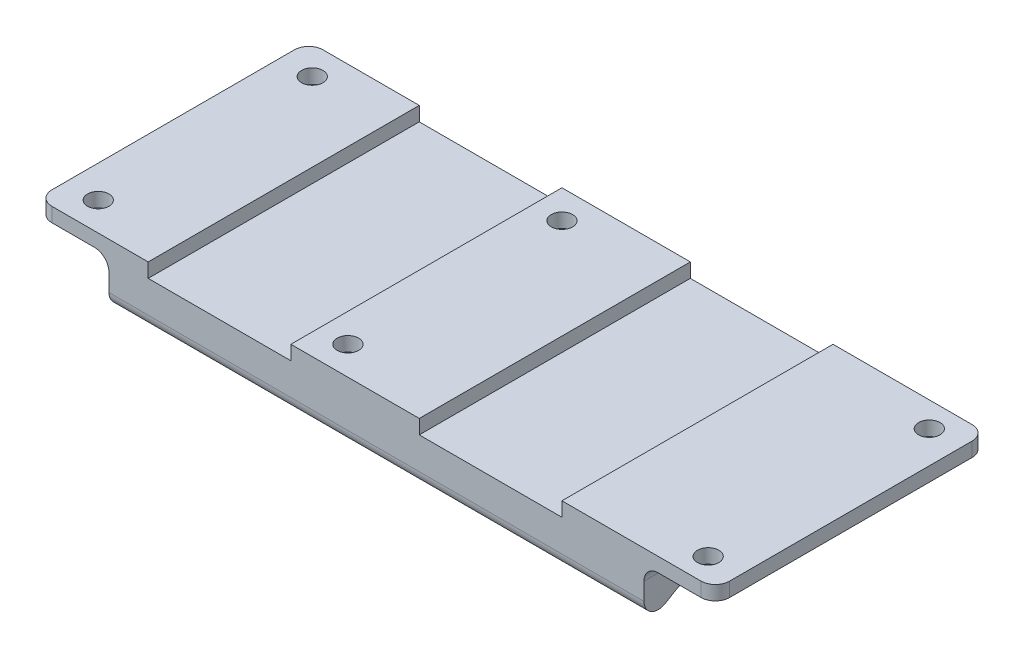
SolidWorks part; units mm, degrees
material "PEI"
ref_plane "Front Plane" through (0, 0, 0) normal (0, 0, 1) x (1, 0, 0)
ref_plane "Top Plane" through (0, 0, 0) normal (0, 1, 0) x (1, 0, 0)
ref_plane "Right Plane" through (0, 0, 0) normal (1, 0, 0) x (0, 0, -1)
sketch "Sketch1" plane through (0, 0, 0) normal (0, 1, 0) x (1, 0, 0)
  line L1 (45.5, -19) -> (-29.5, -19)
  line L2 (45.5, -19) -> (45.5, 19)
  line L3 (45.5, 19) -> (-29.5, 19)
  line L4 (-29.5, -19) -> (-29.5, 19)
  line L5 (45.5, -19) -> (-29.5, 19) construction
  line L6 (45.5, 19) -> (-29.5, -19) construction
  point P0 (8, 0)
  point P6 (0, 0)
  point P7 (14.5588, 3.1563)
  point P9 (0, 0)
  dimension "D1" = 38
  dimension "D2" = 75
  dimension "D3" = 8
extrude "Boss-Extrude1" add sketch "Sketch1" against normal blind 10
sketch "Sketch2" plane through (45.5, 0, 0) normal (1, 0, 0) x (0, 0, -1)
  line L0 (-19, -10) -> (-14, -7)
  line L1 (-14, -7) -> (14, -7)
  line L2 (0, -7) -> (0, -10)
  line L3 (19, -10) -> (14, -7)
  line L4 (19, 0) -> (-19, 0)
  line L5 (-19, 0) -> (-19, -10)
  line L6 (-19, -10) -> (19, -10)
  line L7 (19, -10) -> (19, 0)
  line L8 (19, 0) -> (-19, 0)
  line L9 (-19, 0) -> (-19, -10)
  line L10 (-19, -10) -> (19, -10)
  line L11 (19, -10) -> (19, 0)
  line M7 (-19, -10) -> (19, -10)
  dimension "D2" = 5
  dimension "D3" = 3
  dimension "D1" = 0
extrude "Cut-Extrude1" cut sketch "Sketch2" against normal through all and the other way through all contours L2 L1 L0 M7 | L3 L1 L2 M7
fillet "Fillet1" radius 2 4 edges at (8, -7, 14) (8, -7, -14) (8, -10, -19) (8, -10, 19)
sketch "Sketch4" plane through (-29.5, 0, 0) normal (-1, 0, 0) x (0, 0, 1)
  line L1 (-19, 0) -> (19, 0)
  line L2 (-19, 0) -> (-19, -2)
  line L3 (-19, -2) -> (19, -2)
  line L4 (19, 0) -> (19, -2)
  line L6 (-19, 0) -> (-19, -6.4676)
  line L7 (-15.971, -8.1826) -> (-14.475, -7.285)
  line L11 (19, 0) -> (-19, 0)
  line L12 (-19, 0) -> (-19, -6.4676)
  line L13 (-15.971, -8.1826) -> (-14.475, -7.285)
  line L17 (19, 0) -> (-19, 0)
  line L19 (-13.446, -7) -> (13.446, -7)
  line L20 (-13.446, -7) -> (13.446, -7)
  line L21 (14.475, -7.285) -> (15.971, -8.1826)
  line L22 (14.475, -7.285) -> (15.971, -8.1826)
  line L23 (19, -6.4676) -> (19, 0)
  line L24 (19, -6.4676) -> (19, 0)
  arc A4 (-19, -6.4676) -> (-15.971, -8.1826) centre (-17, -6.4676) ccw
  arc A5 (-19, -6.4676) -> (-15.971, -8.1826) centre (-17, -6.4676) ccw
  arc A6 (-13.446, -7) -> (-14.475, -7.285) centre (-13.446, -9) ccw
  arc A7 (-13.446, -7) -> (-14.475, -7.285) centre (-13.446, -9) ccw
  arc A12 (14.475, -7.285) -> (13.446, -7) centre (13.446, -9) ccw
  arc A13 (14.475, -7.285) -> (13.446, -7) centre (13.446, -9) ccw
  arc A14 (15.971, -8.1826) -> (19, -6.4676) centre (17, -6.4676) ccw
  arc A15 (15.971, -8.1826) -> (19, -6.4676) centre (17, -6.4676) ccw
  line M12 (-19, 0) -> (-19, -6.4676)
  line M20 (19, -6.4676) -> (19, 0)
  line M21 (19, 0) -> (-19, 0)
  dimension "D2" = 2
  dimension "D1" = 0
extrude "Boss-Extrude2" add sketch "Sketch4" along normal blind 10 contours L3 M12 M20 M21
sketch "Sketch5" plane through (45.5, 0, 0) normal (1, 0, 0) x (0, 0, -1)
  line L1 (-19, 0) -> (19, 0)
  line L2 (-19, 0) -> (-19, -2)
  line L3 (-19, -2) -> (19, -2)
  line L4 (19, 0) -> (19, -2)
  line L6 (14.475, -7.285) -> (15.971, -8.1826)
  line L7 (19, -6.4676) -> (19, 0)
  line L8 (19, 0) -> (-19, 0)
  line L12 (14.475, -7.285) -> (15.971, -8.1826)
  line L13 (19, -6.4676) -> (19, 0)
  line L14 (19, 0) -> (-19, 0)
  line L19 (-19, 0) -> (-19, -6.4676)
  line L20 (-19, 0) -> (-19, -6.4676)
  line L21 (-15.971, -8.1826) -> (-14.475, -7.285)
  line L22 (-15.971, -8.1826) -> (-14.475, -7.285)
  line L23 (-13.446, -7) -> (13.446, -7)
  line L24 (-13.446, -7) -> (13.446, -7)
  arc A4 (15.971, -8.1826) -> (19, -6.4676) centre (17, -6.4676) ccw
  arc A5 (15.971, -8.1826) -> (19, -6.4676) centre (17, -6.4676) ccw
  arc A6 (-19, -6.4676) -> (-15.971, -8.1826) centre (-17, -6.4676) ccw
  arc A7 (-19, -6.4676) -> (-15.971, -8.1826) centre (-17, -6.4676) ccw
  arc A12 (-13.446, -7) -> (-14.475, -7.285) centre (-13.446, -9) ccw
  arc A13 (-13.446, -7) -> (-14.475, -7.285) centre (-13.446, -9) ccw
  arc A14 (14.475, -7.285) -> (13.446, -7) centre (13.446, -9) ccw
  arc A15 (14.475, -7.285) -> (13.446, -7) centre (13.446, -9) ccw
  line M14 (19, -6.4676) -> (19, 0)
  line M15 (19, 0) -> (-19, 0)
  line M16 (-19, 0) -> (-19, -6.4676)
  dimension "D2" = 2
  dimension "D1" = 0
extrude "Boss-Extrude3" add sketch "Sketch5" along normal blind 10 contours L3 M16 M14 M15
sketch "Sketch6" plane through (0, 0, 0) normal (0, 1, 0) x (1, 0, 0)
  line L0 (0, 0) -> (55.5, 0)
  line L1 (51, 0) -> (51, 15.5)
  line L2 (0, 0) -> (0, 15)
  line L3 (0, 15) -> (-35, 15)
  line L4 (55.5, 19) -> (-39.5, 19)
  line L5 (-39.5, 19) -> (-39.5, -19)
  line L6 (-39.5, -19) -> (55.5, -19)
  line L7 (55.5, -19) -> (55.5, 19)
  line L8 (55.5, 19) -> (-39.5, 19)
  line L9 (-39.5, 19) -> (-39.5, -19)
  line L10 (-39.5, -19) -> (55.5, -19)
  line L11 (55.5, -19) -> (55.5, 19)
  circle A0 centre (51, 15.5) radius 1.5
  circle A1 centre (-35, 15) radius 1.5
  circle A2 centre (0, 15) radius 1.5
  circle A3 centre (-35, -15) radius 1.5
  circle A4 centre (0, -15) radius 1.5
  circle A5 centre (51, -15.5) radius 1.5
  point P15 (-27.3517, 15.5)
  point P22 (0, 0)
  point P23 (0, 0)
  point P24 (-35, 15.458)
  dimension "D2" = 3
  dimension "D7" = 3
  dimension "D8" = 3
  dimension "D3" = 15.5
  dimension "D4" = 51
  dimension "D5" = 15
  dimension "D9" = 35
  dimension "D1" = 0
extrude "Cut-Extrude2" cut sketch "Sketch6" against normal blind 10
sketch "Sketch8" plane through (0, 0, 0) normal (0, 1, 0) x (1, 0, 0)
  line L0 (0, 0) -> (55.5, 0)
  line L4 (55.5, 19) -> (-39.5, 19)
  line L5 (-39.5, 19) -> (-39.5, -19)
  line L6 (-39.5, -19) -> (55.5, -19)
  line L7 (55.5, -19) -> (55.5, 19)
  line L8 (55.5, 19) -> (-39.5, 19)
  line L9 (-39.5, 19) -> (-39.5, -19)
  line L10 (-39.5, -19) -> (55.5, -19)
  line L11 (55.5, -19) -> (55.5, 19)
  circle A0 centre (0, -15) radius 2.75
  circle A1 centre (0, 15) radius 2.75
  circle M14 centre (0, 15) radius 1.5
  circle M15 centre (0, -15) radius 1.5
  dimension "D2" = 5.5
  dimension "D1" = 0
extrude "Cut-Extrude3" cut sketch "Sketch8" against normal through all from offset 2 contours A0 M15 | A1 M14 offset against normal yes
fillet "Fillet2" radius 0.2 12 edges at (-2.7402, -7.7391, -15.2318) (2.7402, -7.7391, -15.2318) (-2.5435, -7.0657, -13.9545) (2.5936, -7.1051, -14.0858) (0, -7, -12.25) (-2.7402, -7.7391, 15.2318) (2.7402, -7.7391, 15.2318) (-2.5435, -7.0657, 13.9545) (2.5936, -7.1051, 14.0858) (0, -7, 12.25) (-0.5327, -4.5933, -17.6979) (0.8292, -8.3684, 17.622)
sketch "Sketch9" plane through (0, 0, 19) normal (0, 0, 1) x (1, 0, 0)
  line L0 (0, 0) -> (0, -6.4676)
  line L1 (0, 0) -> (-14, 0)
  line L2 (0, 0) -> (24, 0)
  line L3 (-24, 2) -> (-4, 2)
  line L4 (-24, 2) -> (-24, -2)
  line L5 (-24, -2) -> (-4, -2)
  line L6 (-4, 2) -> (-4, -2)
  line L7 (-24, 2) -> (-4, -2) construction
  line L8 (-29.5, -2) -> (-29.5, -6.4676)
  line L9 (-29.5, -6.4676) -> (45.5, -6.4676)
  line L10 (45.5, -6.4676) -> (45.5, -2)
  line L11 (45.5, -2) -> (55.5, -2)
  line L12 (55.5, -2) -> (55.5, 0)
  line L13 (55.5, 0) -> (-39.5, 0)
  line L14 (-39.5, 0) -> (-39.5, -2)
  line L15 (-39.5, -2) -> (-29.5, -2)
  line L16 (-29.5, -2) -> (-29.5, -6.4676)
  line L17 (-29.5, -6.4676) -> (45.5, -6.4676)
  line L18 (45.5, -6.4676) -> (45.5, -2)
  line L19 (45.5, -2) -> (55.5, -2)
  line L20 (55.5, -2) -> (55.5, 0)
  line L21 (55.5, 0) -> (-39.5, 0)
  line L22 (-39.5, 0) -> (-39.5, -2)
  line L23 (-39.5, -2) -> (-29.5, -2)
  line L24 (-24, -2) -> (-4, 2) construction
  line L26 (34, -2) -> (14, -2)
  line L27 (34, -2) -> (34, 2)
  line L28 (34, 2) -> (14, 2)
  line L29 (14, -2) -> (14, 2)
  line L30 (34, -2) -> (14, 2) construction
  line L31 (34, 2) -> (14, -2) construction
  line M20 (55.5, 0) -> (-39.5, 0)
  dimension "D2" = 14
  dimension "D3" = 20
  dimension "D4" = 4
  dimension "D5" = 24
  dimension "D6" = 20
  dimension "D7" = 4
  dimension "D1" = 0
extrude "Cut-Extrude4" cut sketch "Sketch9" against normal through all contours L6 L1 L4 L5 M20 | L29 L26 L27 L21 M20
fillet "Fillet3" radius 2 6 edges at (55.5, -1, 19) (55.5, -1, -19) (-39.5, -1, -19) (-39.5, -1, 19) (45.5, -2, 0) (-29.5, -2, 0)
